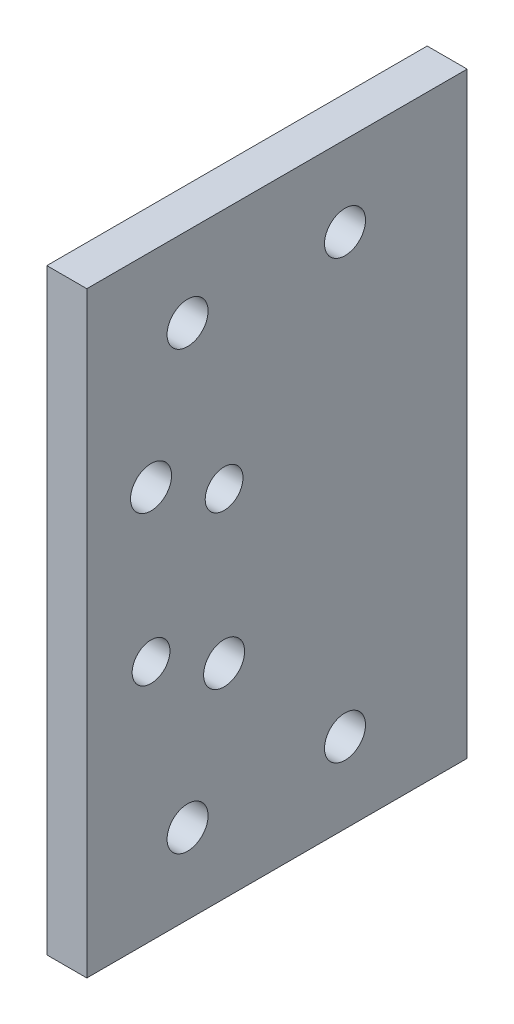
SolidWorks part; units mm, degrees
ref_plane "Front Plane" through (0, 0, 0) normal (1, 0, 0) x (0, 1, 0)
ref_plane "Top Plane" through (0, 0, 0) normal (0, 0, 1) x (0, 1, 0)
ref_plane "Right Plane" through (0, 0, 0) normal (0, 1, 0) x (-1, 0, 0)
sketch "Sketch1" plane through (0, 0, 0) normal (1, 0, 0) x (0, 1, 0)
  line L0 (0, 25) -> (0, -25) construction
  line L1 (-47.4, -25) -> (47.4, -25) construction
  line L2 (-47.4, -25) -> (-47.4, 25) construction
  line L3 (-47.4, 25) -> (47.4, 25) construction
  line L4 (47.4, -25) -> (47.4, 25) construction
  line L5 (-47.4, -25) -> (47.4, 25) construction
  line L6 (-47.4, 25) -> (47.4, -25) construction
  line L13 (-9, 5.8) -> (9, -5.8) construction
  line L14 (-34.7, -15) -> (34.7, -15) construction
  line L15 (-34.7, -15) -> (-34.7, 15) construction
  line L16 (-34.7, 15) -> (34.7, 15) construction
  line L17 (34.7, -15) -> (34.7, 15) construction
  line L18 (-34.7, -15) -> (34.7, 15) construction
  line L19 (-34.7, 15) -> (34.7, -15) construction
  line L20 (-47.4, -25) -> (47.4, -25) construction
  line L21 (-47.4, -25) -> (-47.4, -69.8)
  line L22 (-47.4, -69.8) -> (47.4, -69.8)
  line L23 (47.4, -25) -> (47.4, -69.8) construction
  line L24 (-47.4, -69.8) -> (-34.7, -69.8) construction
  line L25 (-47.4, -69.8) -> (-47.4, -57.1) construction
  line L26 (-47.4, -57.1) -> (-34.7, -57.1) construction
  line L27 (-34.7, -69.8) -> (-34.7, -57.1) construction
  line L28 (47.4, -69.8) -> (34.7, -69.8) construction
  line L29 (47.4, -69.8) -> (47.4, -57.1) construction
  line L30 (47.4, -57.1) -> (34.7, -57.1) construction
  line L31 (34.7, -69.8) -> (34.7, -57.1) construction
  line L34 (47.4, -69.8) -> (47.4, 16)
  line L40 (-47.4, -25) -> (-47.4, 16)
  line L43 (-47.4, 16) -> (47.4, 16)
  line L44 (-47.4, -44.4) -> (47.4, -44.4) construction
  circle A0 centre (-9, 5.8) radius 3
  circle A1 centre (-15, -5.8) radius 3.2576
  circle A2 centre (9, -5.8) radius 3
  circle A3 centre (15, 5.8) radius 3.2576
  circle A4 centre (-34.7, 15) radius 2.555 construction
  circle A5 centre (-34.7, -15) radius 2.555 construction
  circle A6 centre (34.7, 15) radius 2.555 construction
  circle A7 centre (34.7, -15) radius 2.555 construction
  circle A8 centre (-34.7, -57.1) radius 3.2576
  circle A9 centre (34.7, -57.1) radius 3.2576
  circle A10 centre (-34.7, -25) radius 3.2576
  circle A11 centre (-34.7, 0) radius 3.2576
  circle A12 centre (34.7, 0) radius 3.2576
  circle A13 centre (34.7, -25) radius 3.2576
  point P0 (0, 0)
  point P8 (0, 0)
  point P17 (0, 0)
  dimension "D9" = 5.11
  dimension "D10" = 5.11
  dimension "D12" = 6
  dimension "D13" = 6
  dimension "D17" = 6.5151
  dimension "D5" = 6.5151
  dimension "D2" = 24
  dimension "D3" = 94.8
  dimension "D4" = 50
  dimension "D8" = 30
  dimension "D15" = 12.7
  dimension "D16" = 12.7
  dimension "D7" = 12.7
  dimension "D19" = 25.4
  dimension "D14" = 38.6
  dimension "D20" = 10.2
  dimension "D6" = 5.8
  dimension "D11" = 9
  dimension "D18" = 5.8
  dimension "D21" = 24
extrude "Boss-Extrude1" add sketch "Sketch1" along normal blind 6.35
sketch "Sketch2" plane through (6.35, 0, 0) normal (1, 0, 0) x (0, 1, 0)
  line L0 (47.4, -69.8) -> (47.4, 16) construction
  line L1 (-47.4, -69.8) -> (47.4, -69.8)
  line L2 (-47.4, -69.8) -> (-47.4, -44.4)
  line L3 (-47.4, -44.4) -> (47.4, -44.4)
  line L4 (47.4, -69.8) -> (47.4, -44.4)
  dimension "D1" = 25.4
extrude "Cut-Extrude1" cut sketch "Sketch2" against normal up to surface (6.35 mm away) up to face at (0, 34.7, -3.2576)
equation "\"D18@Sketch1\"=\"D6@Sketch1\""
equation "\"D21@Sketch1\"=\"D2@Sketch1\""
